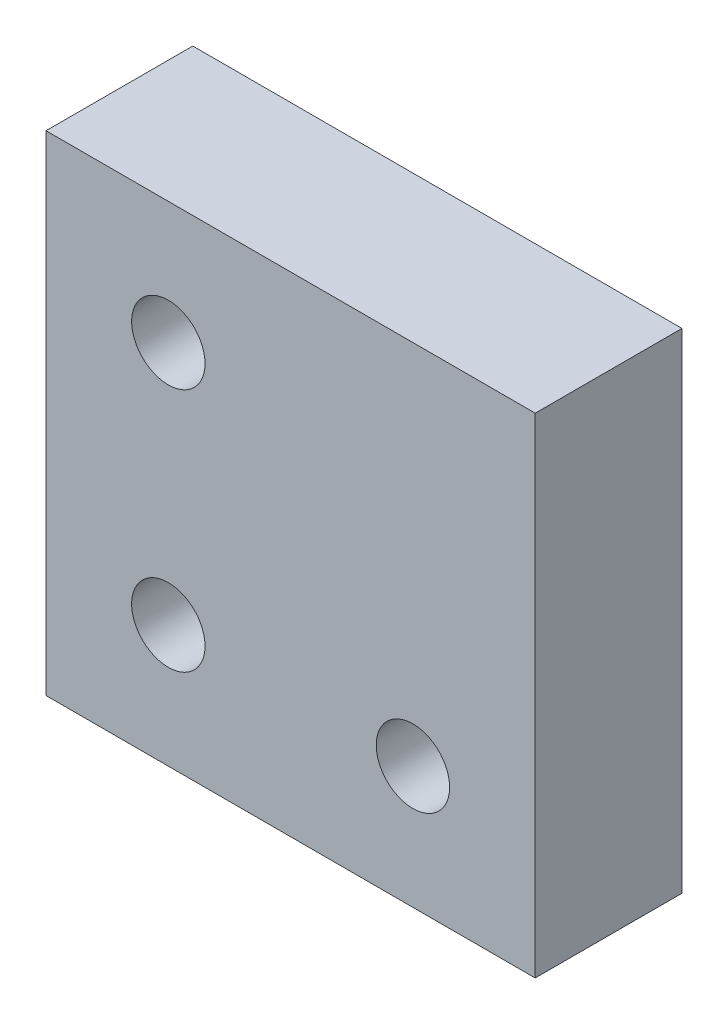
SolidWorks part; units mm, degrees
ref_plane "Plan de face" through (0, 0, 0) normal (0, 0, 1) x (1, 0, 0)
ref_plane "Plan de dessus" through (0, 0, 0) normal (0, 1, 0) x (1, 0, 0)
ref_plane "Plan de droite" through (0, 0, 0) normal (1, 0, 0) x (0, 0, -1)
sketch "Esquisse1" plane through (0, 0, 0) normal (0, 0, 1) x (1, 0, 0)
  line L1 (-10, 10) -> (10, 10)
  line L2 (-10, 10) -> (-10, -10)
  line L3 (-10, -10) -> (10, -10)
  line L4 (10, 10) -> (10, -10)
  dimension "D1" = 20
  dimension "D2" = 20
  dimension "D3" = 10
  dimension "D4" = 10
extrude "Boss.-Extru.1" add sketch "Esquisse1" along normal blind 6
sketch "Esquisse2" plane through (0, 0, 6) normal (0, 0, 1) x (1, 0, 0)
  line L3 (-10, 10) -> (-10, -10) construction
  line L4 (10, 10) -> (-10, 10) construction
  circle A0 centre (-5, 5) radius 1.5
  circle A1 centre (-5, -5) radius 1.5
  circle A2 centre (5, -5) radius 1.5
  dimension "D1" = 3
  dimension "D2" = 10
  dimension "D4" = 3
  dimension "D5" = 3
  dimension "D6" = 5
  dimension "D7" = 5
  dimension "D8" = 5
  dimension "D3" = 15
  dimension "D9" = 10
extrude "Enlèv. mat.-Extru.1" cut sketch "Esquisse2" against normal blind 6
equation "\"D3@Esquisse1\"=\"D2@Esquisse1\"/2"
equation "\"D4@Esquisse1\"=\"D1@Esquisse1\"/2"
